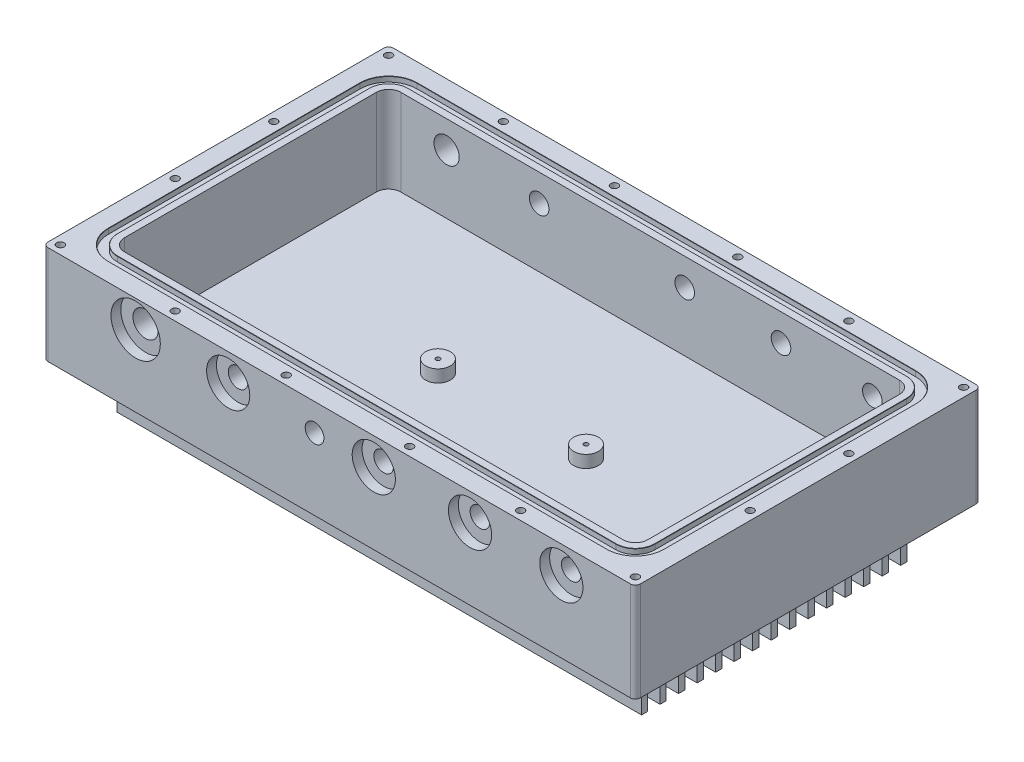
SolidWorks part; units mm, degrees
material "6061 Alloy"
ref_plane "Front Plane" through (0, 0, 0) normal (0, 0, 1) x (1, 0, 0)
ref_plane "Top Plane" through (0, 0, 0) normal (0, 1, 0) x (1, 0, 0)
ref_plane "Right Plane" through (0, 0, 0) normal (1, 0, 0) x (0, 0, -1)
sketch "Sketch1" plane through (0, 0, 0) normal (0, 1, 0) x (1, 0, 0)
  line L1 (0, 0) -> (304.8, 0)
  line L2 (0, 0) -> (0, 177.8)
  line L3 (0, 177.8) -> (304.8, 177.8)
  line L4 (304.8, 0) -> (304.8, 177.8)
  dimension "D1" = 304.8
  dimension "D2" = 177.8
extrude "Boss-Extrude1" add sketch "Sketch1" along normal blind 76.2
sketch "Sketch2" plane through (0, 76.2, 0) normal (0, 1, 0) x (1, 0, 0)
  line L14 (17.78, 17.78) -> (287.02, 17.78)
  line L15 (287.02, 17.78) -> (287.02, 160.02)
  line L16 (287.02, 160.02) -> (17.78, 160.02)
  line L17 (17.78, 160.02) -> (17.78, 17.78)
  line L18 (17.78, 17.78) -> (287.02, 17.78)
  line L19 (287.02, 17.78) -> (287.02, 160.02)
  line L20 (287.02, 160.02) -> (17.78, 160.02)
  line L21 (17.78, 160.02) -> (17.78, 17.78)
  dimension "D1" = 17.78
extrude "Cut-Extrude1" cut sketch "Sketch2" against normal blind 38.1
sketch "Sketch3" plane through (0, 0, 0) normal (0, -1, 0) x (1, 0, 0)
  line L0 (304.8, -177.8) -> (0, -177.8) construction
  line L1 (304.8, 0) -> (304.8, -177.8) construction
  line L2 (0, 0) -> (304.8, 0) construction
  line L3 (0, -177.8) -> (0, 0) construction
  line L4 (304.8, -177.8) -> (0, -177.8)
  line L5 (304.8, 0) -> (304.8, -177.8)
  line L6 (0, 0) -> (304.8, 0)
  line L7 (0, -177.8) -> (0, 0)
  line L8 (17.4625, -160.3375) -> (17.4625, -17.4625)
  line L9 (17.4625, -17.4625) -> (287.3375, -17.4625)
  line L10 (287.3375, -17.4625) -> (287.3375, -160.3375)
  line L11 (287.3375, -160.3375) -> (17.4625, -160.3375)
  dimension "D1" = 17.4625
extrude "Cut-Extrude2" cut sketch "Sketch3" against normal blind 25.4
sketch "Sketch4" plane through (287.3375, 0, 0) normal (1, 0, 0) x (0, 0, -1)
  line L0 (88.9, 0) -> (88.9, 25.4) construction
  line L1 (160.3375, 0) -> (17.4625, 0) construction
  line L2 (160.3375, 25.4) -> (17.4625, 25.4) construction
  line L3 (87.3125, 0) -> (90.4875, 0)
  line L4 (90.4875, 0) -> (90.4875, 25.4)
  line L5 (177.8, 25.4) -> (0, 25.4) construction
  line L6 (90.4875, 25.4) -> (96.8375, 25.4)
  line L7 (96.8375, 25.4) -> (96.8375, 0)
  line L8 (96.8375, 0) -> (100.0125, 0)
  line L9 (100.0125, 0) -> (100.0125, 25.4)
  line L10 (100.0125, 25.4) -> (106.3625, 25.4)
  line L11 (106.3625, 25.4) -> (106.3625, 0)
  line L12 (106.3625, 0) -> (109.5375, 0)
  line L13 (109.5375, 0) -> (109.5375, 25.4)
  line L14 (109.5375, 25.4) -> (115.8875, 25.4)
  line L15 (115.8875, 25.4) -> (115.8875, 0)
  line L16 (115.8875, 0) -> (119.0625, 0)
  line L17 (119.0625, 0) -> (119.0625, 25.4)
  line L18 (119.0625, 25.4) -> (125.4125, 25.4)
  line L19 (125.4125, 25.4) -> (125.4125, 0)
  line L20 (125.4125, 0) -> (128.5875, 0)
  line L21 (128.5875, 0) -> (128.5875, 25.4)
  line L22 (128.5875, 25.4) -> (134.9375, 25.4)
  line L23 (134.9375, 25.4) -> (134.9375, 0)
  line L24 (134.9375, 0) -> (138.1125, 0)
  line L25 (138.1125, 0) -> (138.1125, 25.4)
  line L26 (138.1125, 25.4) -> (144.4625, 25.4)
  line L27 (144.4625, 25.4) -> (144.4625, 0)
  line L28 (144.4625, 0) -> (147.6375, 0)
  line L29 (147.6375, 0) -> (147.6375, 25.4)
  line L30 (147.6375, 25.4) -> (153.9875, 25.4)
  line L31 (153.9875, 25.4) -> (153.9875, 0)
  line L32 (153.9875, 0) -> (157.1625, 0)
  line L33 (157.1625, 0) -> (157.1625, 25.4)
  line L34 (157.1625, 25.4) -> (163.5125, 25.4)
  line L35 (163.5125, 25.4) -> (163.5125, 0)
  line L36 (163.5125, 0) -> (166.6875, 0)
  line L37 (166.6875, 0) -> (166.6875, 25.4)
  line L38 (166.6875, 25.4) -> (173.0375, 25.4)
  line L39 (173.0375, 25.4) -> (173.0375, 0)
  line L40 (4.7625, 25.4) -> (4.7625, 0)
  line L41 (11.1125, 25.4) -> (4.7625, 25.4)
  line L42 (11.1125, 0) -> (11.1125, 25.4)
  line L43 (14.2875, 0) -> (11.1125, 0)
  line L44 (14.2875, 25.4) -> (14.2875, 0)
  line L45 (20.6375, 25.4) -> (14.2875, 25.4)
  line L46 (20.6375, 0) -> (20.6375, 25.4)
  line L47 (23.8125, 0) -> (20.6375, 0)
  line L48 (23.8125, 25.4) -> (23.8125, 0)
  line L49 (30.1625, 25.4) -> (23.8125, 25.4)
  line L50 (30.1625, 0) -> (30.1625, 25.4)
  line L51 (33.3375, 0) -> (30.1625, 0)
  line L52 (33.3375, 25.4) -> (33.3375, 0)
  line L53 (39.6875, 25.4) -> (33.3375, 25.4)
  line L54 (39.6875, 0) -> (39.6875, 25.4)
  line L55 (42.8625, 0) -> (39.6875, 0)
  line L56 (42.8625, 25.4) -> (42.8625, 0)
  line L57 (49.2125, 25.4) -> (42.8625, 25.4)
  line L58 (49.2125, 0) -> (49.2125, 25.4)
  line L59 (52.3875, 0) -> (49.2125, 0)
  line L60 (52.3875, 25.4) -> (52.3875, 0)
  line L61 (58.7375, 25.4) -> (52.3875, 25.4)
  line L62 (58.7375, 0) -> (58.7375, 25.4)
  line L63 (61.9125, 0) -> (58.7375, 0)
  line L64 (61.9125, 25.4) -> (61.9125, 0)
  line L65 (68.2625, 25.4) -> (61.9125, 25.4)
  line L66 (68.2625, 0) -> (68.2625, 25.4)
  line L67 (71.4375, 0) -> (68.2625, 0)
  line L68 (71.4375, 25.4) -> (71.4375, 0)
  line L69 (77.7875, 25.4) -> (71.4375, 25.4)
  line L70 (77.7875, 0) -> (77.7875, 25.4)
  line L71 (80.9625, 0) -> (77.7875, 0)
  line L72 (80.9625, 25.4) -> (80.9625, 0)
  line L73 (87.3125, 25.4) -> (80.9625, 25.4)
  line L74 (87.3125, 0) -> (87.3125, 25.4)
  line L75 (173.0375, 0) -> (176.2125, 0)
  line L76 (176.2125, 0) -> (176.2125, 25.4)
  line L77 (176.2125, 25.4) -> (182.5625, 25.4)
  line L78 (182.5625, 25.4) -> (182.5625, 0)
  line L79 (182.5625, 0) -> (185.7375, 0)
  line L80 (185.7375, 0) -> (185.7375, 25.4)
  line L81 (185.7375, 25.4) -> (192.0875, 25.4)
  line L82 (192.0875, 25.4) -> (192.0875, 0)
  line L83 (192.0875, 0) -> (195.2625, 0)
  line L84 (195.2625, 0) -> (195.2625, 25.4)
  line L85 (195.2625, 25.4) -> (201.6125, 25.4)
  line L86 (201.6125, 25.4) -> (201.6125, 0)
  line L87 (201.6125, 0) -> (204.7875, 0)
  line L88 (204.7875, 0) -> (204.7875, 25.4)
  line L89 (204.7875, 25.4) -> (211.1375, 25.4)
  line L90 (-42.8625, 0) -> (-46.0375, 0)
  line L91 (4.7625, 0) -> (1.5875, 0)
  line L92 (-42.8625, 25.4) -> (-42.8625, 0)
  line L93 (211.1375, 25.4) -> (211.1375, 0)
  line L94 (-26.9875, 0) -> (-26.9875, 25.4)
  line L95 (-23.8125, 0) -> (-26.9875, 0)
  line L96 (-23.8125, 25.4) -> (-23.8125, 0)
  line L97 (-17.4625, 25.4) -> (-23.8125, 25.4)
  line L98 (-17.4625, 0) -> (-17.4625, 25.4)
  line L99 (-14.2875, 0) -> (-17.4625, 0)
  line L100 (-14.2875, 25.4) -> (-14.2875, 0)
  line L101 (-7.9375, 25.4) -> (-14.2875, 25.4)
  line L102 (-7.9375, 0) -> (-7.9375, 25.4)
  line L103 (-4.7625, 0) -> (-7.9375, 0)
  line L104 (-4.7625, 25.4) -> (-4.7625, 0)
  line L105 (1.5875, 25.4) -> (-4.7625, 25.4)
  line L106 (1.5875, 0) -> (1.5875, 25.4)
  line L107 (-36.5125, 25.4) -> (-42.8625, 25.4)
  line L108 (211.1375, 0) -> (214.3125, 0)
  line L109 (214.3125, 0) -> (214.3125, 25.4)
  line L110 (214.3125, 25.4) -> (220.6625, 25.4)
  line L111 (220.6625, 25.4) -> (220.6625, 0)
  line L112 (220.6625, 0) -> (223.8375, 0)
  line L113 (223.8375, 0) -> (223.8375, 25.4)
  line L114 (223.8375, 25.4) -> (230.1875, 25.4)
  line L115 (230.1875, 25.4) -> (230.1875, 0)
  line L116 (-36.5125, 0) -> (-36.5125, 25.4)
  line L117 (-33.3375, 0) -> (-36.5125, 0)
  line L118 (-33.3375, 25.4) -> (-33.3375, 0)
  line L119 (-26.9875, 25.4) -> (-33.3375, 25.4)
  line L120 (-46.0375, 0) -> (-46.0375, 25.4)
  line L121 (-46.0375, 25.4) -> (-52.3875, 25.4)
  line L122 (-52.3875, 25.4) -> (-52.3875, 0)
  line L123 (-52.3875, 0) -> (-52.3875, -16.0515)
  line L124 (-52.3875, -16.0515) -> (230.1875, -16.0515)
  line L125 (230.1875, -16.0515) -> (230.1875, 0)
  dimension "D1" = 1.5875
  dimension "D2" = 3.175
  dimension "D3" = 6.35
extrude "Cut-Extrude3" cut sketch "Sketch4" against normal through all
sketch "Sketch5" plane through (0, 76.2, 0) normal (0, 1, 0) x (1, 0, 0)
  line L0 (304.8, 88.9) -> (0, 88.9) construction
  line L1 (304.8, 0) -> (304.8, 177.8) construction
  line L2 (0, 177.8) -> (0, 0) construction
  line L3 (152.4, 177.8) -> (152.4, 0) construction
  line L4 (304.8, 177.8) -> (0, 177.8) construction
  line L5 (0, 0) -> (304.8, 0) construction
  line L6 (304.8, 173.355) -> (152.4, 173.355) construction
  line L7 (300.355, 177.8) -> (300.355, 0) construction
  point P21 (184.15, 173.355)
  point P33 (241.3, 173.355)
  point P34 (300.355, 173.355)
  point P36 (120.65, 4.445)
  point P37 (63.5, 4.445)
  point P38 (4.445, 4.445)
  point P39 (300.355, 114.3)
  point P41 (4.445, 63.5)
  point P42 (4.445, 114.3)
  point P43 (4.445, 173.355)
  point P44 (63.5, 173.355)
  point P46 (184.15, 4.445)
  point P47 (120.65, 173.355)
  point P51 (300.355, 4.445)
  point P52 (300.355, 63.5)
  point P53 (241.3, 4.445)
  dimension "D1" = 31.75
  dimension "D3" = 25.4
  dimension "D2" = 88.9
  dimension "D4" = 4.445
  dimension "D5" = 4.445
hole_wizard "#10-24 Tapped Hole1" positions "Sketch28" profile "Sketch29" tap size "#10-24" standard "ANSI Inch"
sketch "Sketch28" plane through (0, 76.2, 0) normal (0, 1, 0) x (1, 0, 0)
  point P0 (63.5, 173.355)
  point P3 (120.65, 173.355)
  point P6 (184.15, 173.355)
  point P9 (241.3, 173.355)
  point P15 (241.3, 4.445)
  point P18 (184.15, 4.445)
  point P21 (120.65, 4.445)
  point P24 (63.5, 4.445)
sketch "Sketch29" plane through (63.5, 76.2, -173.355) normal (1, 0, 0) x (0, 0, 1)
  line L0 (0, 0) -> (0, 16.1014)
  line L1 (0, 16.1014) -> (1.8986, 14.9606)
  line L2 (1.8986, 14.9606) -> (1.8986, 0)
  line L5 (1.8986, 0) -> (0, 0)
  line L10 (0, 16.1014) -> (-1.8987, 14.9606) construction
  line L11 (0, -6.35) -> (0, 107.95) construction
  dimension "Tap Drill Dia." = 3.7973
  dimension "Tap Drill Depth" = 14.9606
  dimension "Drill Angle" = 118
cosmetic thread "Hole Thread1" parameters "D1"=9.652, "D2"=4.826
cosmetic thread "Hole Thread2" parameters "D1"=9.652, "D2"=4.826
cosmetic thread "Hole Thread3" parameters "D1"=9.652, "D2"=4.826
cosmetic thread "Hole Thread4" parameters "D1"=9.652, "D2"=4.826
cosmetic thread "Hole Thread5" parameters "D1"=9.652, "D2"=4.826
cosmetic thread "Hole Thread6" parameters "D1"=9.652, "D2"=4.826
cosmetic thread "Hole Thread7" parameters "D1"=9.652, "D2"=4.826
cosmetic thread "Hole Thread8" parameters "D1"=9.652, "D2"=4.826
hole_wizard "#10-24 Tapped Hole2" positions "Sketch30" profile "Sketch31" tap size "#10-24" standard "ANSI Inch" end condition through all
sketch "Sketch30" plane through (0, 76.2, 0) normal (0, 1, 0) x (1, 0, 0)
  point P0 (4.445, 173.355)
  point P3 (4.445, 114.3)
  point P6 (4.445, 63.5)
  point P9 (4.445, 4.445)
  point P12 (300.355, 173.355)
  point P15 (300.355, 114.3)
  point P18 (300.355, 63.5)
  point P21 (300.355, 4.445)
sketch "Sketch31" plane through (4.445, 76.2, -173.355) normal (1, 0, 0) x (0, 0, 1)
  line L0 (0, 0) -> (0, 76.2)
  line L1 (0, 76.2) -> (1.8986, 76.2)
  line L2 (1.8986, 76.2) -> (1.8986, 0)
  line L5 (1.8986, 0) -> (0, 0)
  line L11 (0, -6.35) -> (0, 107.95) construction
  dimension "Thru Tap Drill Dia." = 3.7973
  dimension "Thru Tap Drill Depth" = 76.2
cosmetic thread "Hole Thread9" parameters "D2"=4.826
cosmetic thread "Hole Thread10" parameters "D2"=4.826
cosmetic thread "Hole Thread11" parameters "D2"=4.826
cosmetic thread "Hole Thread12" parameters "D2"=4.826
cosmetic thread "Hole Thread13" parameters "D2"=4.826
cosmetic thread "Hole Thread14" parameters "D2"=4.826
cosmetic thread "Hole Thread15" parameters "D2"=4.826
cosmetic thread "Hole Thread16" parameters "D2"=4.826
sketch "Sketch6" plane through (0, 25.4, 0) normal (0, -1, 0) x (1, 0, 0)
  line L0 (152.4, 0) -> (152.4, -177.8) construction
  line L1 (304.8, 0) -> (0, 0) construction
  line L2 (0, -177.8) -> (304.8, -177.8) construction
  line L3 (298.45, 0) -> (298.45, -177.8) construction
  line L4 (304.8, -88.9) -> (287.3375, -88.9) construction
  line L5 (304.8, -177.8) -> (304.8, 0) construction
  line L6 (287.3375, -90.4875) -> (287.3375, -87.3125) construction
  circle A0 centre (298.45, -63.5) radius 1.9558
  circle A1 centre (298.45, -6.35) radius 1.9558
  circle A2 centre (298.45, -171.45) radius 1.9558
  circle A3 centre (6.35, -171.45) radius 1.9558
  circle A5 centre (6.35, -6.35) radius 1.9558
  circle A6 centre (298.45, -114.3) radius 1.9558
  circle A7 centre (6.35, -114.3) radius 1.9558
  circle A8 centre (6.35, -63.5) radius 1.9558
  dimension "D3" = 3.9116
  dimension "D4" = 57.15
  dimension "D1" = 6.35
  dimension "D2" = 6.35
extrude "Cut-Extrude5" [suppressed] cut sketch "Sketch6" against normal blind 25.4
sketch "Sketch7" plane through (0, 0, 0) normal (-1, 0, 0) x (0, 0, 1)
  line L0 (-88.9, 76.2) -> (-88.9, 38.1) construction
  line L2 (-177.8, 76.2) -> (0, 76.2) construction
  line L3 (-160.02, 38.1) -> (-17.78, 38.1) construction
  line L4 (-134.62, 64.77) -> (-17.78, 64.77) construction
  circle A4 centre (-139.7, 64.77) radius 4.3053
  dimension "D1" = 50.8
  dimension "D2" = 8.6106
  dimension "D4" = 11.43
extrude "Cut-Extrude6" [suppressed] cut sketch "Sketch7" against normal blind 25.4
sketch "Sketch9" plane through (0, 0, -177.8) normal (0, 0, -1) x (-1, 0, 0)
  line L0 (-287.02, 62.23) -> (-53.34, 62.23) construction
  line L1 (-152.4, 76.2) -> (-152.4, 25.4) construction
  line L2 (0, 25.4) -> (-304.8, 25.4) construction
  line L3 (-304.8, 76.2) -> (0, 76.2) construction
  circle A2 centre (-47.625, 62.23) radius 5.4991
  point P19 (-266.7, 62.23)
  point P20 (-219.71, 62.23)
  point P21 (-170.18, 62.23)
  point P22 (-95.25, 62.23)
  point P23 (-47.625, 62.23)
  dimension "D1" = 17.78
  dimension "D6" = 57.15
  dimension "D2" = 104.775
  dimension "D3" = 67.31
  dimension "D4" = 13.97
  dimension "D5" = 114.3
fillet "Fillet1" radius 6.35 4 edges at (17.78, 57.15, -160.02) (17.78, 57.15, -17.78) (287.02, 57.15, -160.02) (287.02, 57.15, -17.78)
sketch "Sketch10" plane through (0, 76.2, 0) normal (0, 1, 0) x (1, 0, 0)
  line L20 (280.67, 168.3258) -> (24.13, 168.3258)
  line L21 (9.4742, 153.67) -> (9.4742, 24.13)
  line L22 (24.13, 9.4742) -> (280.67, 9.4742)
  line L23 (295.3258, 24.13) -> (295.3258, 153.67)
  line L24 (14.097, 153.67) -> (14.097, 24.13)
  line L25 (24.13, 14.097) -> (280.67, 14.097)
  line L26 (290.703, 24.13) -> (290.703, 153.67)
  line L27 (280.67, 163.703) -> (24.13, 163.703)
  line L28 (14.097, 153.67) -> (14.097, 24.13)
  line L29 (24.13, 14.097) -> (280.67, 14.097)
  line L30 (290.703, 24.13) -> (290.703, 153.67)
  line L31 (280.67, 163.703) -> (24.13, 163.703)
  arc A16 (295.3258, 153.67) -> (280.67, 168.3258) centre (280.67, 153.67) ccw
  arc A17 (24.13, 168.3258) -> (9.4742, 153.67) centre (24.13, 153.67) ccw
  arc A18 (9.4742, 24.13) -> (24.13, 9.4742) centre (24.13, 24.13) ccw
  arc A19 (280.67, 9.4742) -> (295.3258, 24.13) centre (280.67, 24.13) ccw
  arc A20 (24.13, 163.703) -> (14.097, 153.67) centre (24.13, 153.67) ccw
  arc A21 (14.097, 24.13) -> (24.13, 14.097) centre (24.13, 24.13) ccw
  arc A22 (280.67, 14.097) -> (290.703, 24.13) centre (280.67, 24.13) ccw
  arc A23 (290.703, 153.67) -> (280.67, 163.703) centre (280.67, 153.67) ccw
  arc A24 (24.13, 163.703) -> (14.097, 153.67) centre (24.13, 153.67) ccw
  arc A25 (14.097, 24.13) -> (24.13, 14.097) centre (24.13, 24.13) ccw
  arc A26 (280.67, 14.097) -> (290.703, 24.13) centre (280.67, 24.13) ccw
  arc A27 (290.703, 153.67) -> (280.67, 163.703) centre (280.67, 153.67) ccw
  dimension "D1" = 3.683
  dimension "D2" = 4.6228
extrude "Cut-Extrude9" cut sketch "Sketch10" against normal blind 2.6416
sketch "Sketch11" plane through (0, 76.2, 0) normal (0, 1, 0) x (1, 0, 0)
  line L0 (152.4, 177.8) -> (152.4, 0) construction
  line L1 (304.8, 177.8) -> (0, 177.8) construction
  line L2 (0, 0) -> (304.8, 0) construction
  line L3 (304.8, 88.9) -> (0, 88.9) construction
  line L4 (304.8, 0) -> (304.8, 177.8) construction
  line L5 (0, 177.8) -> (0, 0) construction
  circle A0 centre (293.37, 166.37) radius 1.9558
  circle A1 centre (293.37, 11.43) radius 1.9558
  circle A2 centre (11.43, 11.43) radius 1.9558
  circle A3 centre (11.43, 166.37) radius 1.9558
  dimension "D1" = 3.9116
  dimension "D2" = 11.43
  dimension "D3" = 11.43
extrude "Cut-Extrude10" [suppressed] cut sketch "Sketch11" against normal blind 25.4
hole_wizard "CBORE for 3/8 Hex Head Bolt2" positions "Sketch20" profile "Sketch21" counterbore size "3/8" standard "ANSI Inch" end condition up to next
sketch "Sketch20" plane through (0, 0, -177.8) normal (0, 0, -1) x (-1, 0, 0)
  point P3 (-266.7, 62.23)
  point P6 (-219.71, 62.23)
  point P9 (-170.18, 62.23)
  point P12 (-95.25, 62.23)
sketch "Sketch21" plane through (266.7, 62.23, -177.8) normal (1, 0, 0) x (0, 1, 0)
  line L0 (0, 0) -> (0, 17.78)
  line L1 (0, 17.78) -> (5.0419, 17.78)
  line L3 (5.0419, 17.78) -> (5.0419, 5.08)
  line L4 (5.0419, 5.08) -> (11.1125, 5.08)
  line L5 (11.1125, 5.08) -> (11.1125, 0)
  line L7 (11.1125, 0) -> (0, 0)
  line L11 (0, -6.35) -> (0, 107.95) construction
  dimension "Thru Hole Dia." = 10.0838
  dimension "Thru Hole Depth" = 17.78
  dimension "C'Bore Dia." = 22.225
  dimension "C'Bore Depth" = 5.08
hole_wizard "CBORE for 1/2 Hex Head Bolt1" positions "Sketch22" profile "Sketch23" counterbore size "1/2" standard "ANSI Inch" end condition up to next
sketch "Sketch22" plane through (0, 0, -177.8) normal (0, 0, -1) x (-1, 0, 0)
  point P0 (-47.625, 62.23)
sketch "Sketch23" plane through (47.625, 62.23, -177.8) normal (1, 0, 0) x (0, 1, 0)
  line L0 (0, 0) -> (0, 17.78)
  line L1 (0, 17.78) -> (6.5024, 17.78)
  line L3 (6.5024, 17.78) -> (6.5024, 5.08)
  line L4 (6.5024, 5.08) -> (12.7, 5.08)
  line L5 (12.7, 5.08) -> (12.7, 0)
  line L7 (12.7, 0) -> (0, 0)
  line L11 (0, -6.35) -> (0, 107.95) construction
  dimension "Thru Hole Dia." = 13.0048
  dimension "Thru Hole Depth" = 17.78
  dimension "C'Bore Dia." = 25.4
  dimension "C'Bore Depth" = 5.08
hole_wizard "CBORE for 3/8 Hex Head Bolt1" positions "Sketch24" profile "Sketch25" counterbore size "3/8" standard "ANSI Inch" end condition up to next
sketch "Sketch24" plane through (0, 0, 0) normal (0, 0, 1) x (1, 0, 0)
  point P10 (95.25, 62.23)
  point P13 (170.18, 62.23)
  point P16 (219.71, 62.23)
  point P19 (266.7, 62.23)
sketch "Sketch25" plane through (95.25, 62.23, 0) normal (1, 0, 0) x (0, -1, 0)
  line L0 (0, 0) -> (0, 17.78)
  line L1 (0, 17.78) -> (5.0419, 17.78)
  line L3 (5.0419, 17.78) -> (5.0419, 5.08)
  line L4 (5.0419, 5.08) -> (11.1125, 5.08)
  line L5 (11.1125, 5.08) -> (11.1125, 0)
  line L7 (11.1125, 0) -> (0, 0)
  line L11 (0, -6.35) -> (0, 107.95) construction
  dimension "Thru Hole Dia." = 10.0838
  dimension "Thru Hole Depth" = 17.78
  dimension "C'Bore Dia." = 22.225
  dimension "C'Bore Depth" = 5.08
sketch "Sketch17" plane through (0, 38.1, 0) normal (0, 1, 0) x (1, 0, 0)
  line L0 (287.02, 88.9) -> (17.78, 88.9) construction
  line L1 (287.02, 24.13) -> (287.02, 153.67) construction
  line L2 (17.78, 153.67) -> (17.78, 24.13) construction
  circle A0 centre (114.3, 88.9) radius 3.175
  circle A1 centre (190.5, 88.9) radius 3.175
  dimension "D1" = 6.35
  dimension "D4" = 76.2
  dimension "D2" = 96.52
  dimension "D3" = 96.52
extrude "Boss-Extrude2" [suppressed] add sketch "Sketch17" along normal blind 38.1
fillet "Fillet2" [suppressed] radius 6.35
chamfer "Chamfer1" distance 0.127 angle 45 16 edges at (295.3258, 76.2, -88.9) (291.0332, 76.2, -164.0332) (291.0332, 76.2, -13.7668) (152.4, 76.2, -168.3258) (152.4, 76.2, -9.4742) (13.7668, 76.2, -164.0332) (13.7668, 76.2, -13.7668) (9.4742, 76.2, -88.9) (290.703, 76.2, -88.9) (287.7644, 76.2, -160.7644) (287.7644, 76.2, -17.0356) (152.4, 76.2, -163.703) (152.4, 76.2, -14.097) (17.0356, 76.2, -160.7644) (17.0356, 76.2, -17.0356) (14.097, 76.2, -88.9)
hole_wizard "1/8 NPT Tapped Hole1" positions "Sketch34" profile "Sketch35" size "1/8" standard "ANSI Inch" end condition up to next
sketch "Sketch34" plane through (0, 0, 0) normal (0, 0, 1) x (1, 0, 0)
  line L0 (152.4, 76.2) -> (152.4, 25.4) construction
  line L1 (0, 76.2) -> (304.8, 76.2) construction
  line L2 (304.8, 25.4) -> (0, 25.4) construction
  point P0 (139.7, 62.23)
  dimension "D1" = 12.7
  dimension "D2" = 13.97
sketch "Sketch35" plane through (139.7, 62.23, 0) normal (1, 0, 0) x (0, -1, 0)
  line L0 (0, 0) -> (0, 17.78)
  line L1 (0, 17.78) -> (4.2164, 17.78)
  line L2 (-4.5374, 9.525) -> (-4.8226, 0) construction
  line L3 (4.2164, 17.78) -> (4.2164, 9.525)
  line L4 (4.2164, 9.525) -> (4.5374, 9.525)
  line L5 (4.5374, 9.525) -> (4.8226, 0)
  line L7 (4.8226, 0) -> (0, 0)
  line L8 (0, -6.35) -> (0, 107.95) construction
  line L11 (-4.2164, 9.525) -> (-4.5374, 9.525) construction
  dimension "Thru Tap Drill Dia." = 8.4328
  dimension "Thru Tap Drill Depth" = 17.78
  dimension "Thread Dia." = 9.6452
  dimension "Thread Angle" = 3.43
  dimension "Thread Depth" = 9.525
cosmetic thread "Hole Thread17" parameters "D1"=9.525, "D2"=10.4428
hole_wizard "#4-40 Tapped Hole1" positions "Sketch36" profile "Sketch37" tap size "#4-40" standard "ANSI Inch"
sketch "Sketch36" plane through (0, 38.1, 0) normal (0, 1, 0) x (1, 0, 0)
  line L0 (152.4, 160.02) -> (152.4, 17.78) construction
  line L1 (280.67, 160.02) -> (24.13, 160.02) construction
  line L2 (24.13, 17.78) -> (280.67, 17.78) construction
  line L4 (17.78, 88.9) -> (287.02, 88.9) construction
  line L5 (17.78, 153.67) -> (17.78, 24.13) construction
  line L6 (287.02, 24.13) -> (287.02, 153.67) construction
  point P0 (114.3, 88.9)
  point P2 (190.5, 88.9)
  dimension "D1" = 76.2
sketch "Sketch37" plane through (114.3, 38.1, -88.9) normal (1, 0, 0) x (0, 0, 1)
  line L0 (0, 0) -> (0, 8.2738)
  line L1 (0, 8.2738) -> (1.1303, 7.5946)
  line L2 (1.1303, 7.5946) -> (1.1303, 0)
  line L5 (1.1303, 0) -> (0, 0)
  line L10 (0, 8.2738) -> (-1.1303, 7.5946) construction
  line L11 (0, -6.35) -> (0, 107.95) construction
  dimension "Tap Drill Dia." = 2.2606
  dimension "Tap Drill Depth" = 7.5946
  dimension "Drill Angle" = 118
cosmetic thread "Hole Thread18" parameters "D1"=5.6896, "D2"=2.8448
cosmetic thread "Hole Thread19" parameters "D1"=5.6896, "D2"=2.8448
sketch "Sketch38" plane through (0, 38.1, 0) normal (0, 1, 0) x (1, 0, 0)
  line L0 (17.78, 153.67) -> (17.78, 24.13) construction
  line L1 (24.13, 17.78) -> (280.67, 17.78) construction
  line L2 (287.02, 24.13) -> (287.02, 153.67) construction
  line L3 (280.67, 160.02) -> (24.13, 160.02) construction
  line L4 (17.78, 153.67) -> (17.78, 24.13)
  line L5 (24.13, 17.78) -> (280.67, 17.78)
  line L6 (287.02, 24.13) -> (287.02, 153.67)
  line L7 (280.67, 160.02) -> (24.13, 160.02)
  arc A0 (24.13, 160.02) -> (17.78, 153.67) centre (24.13, 153.67) ccw construction
  arc A1 (17.78, 24.13) -> (24.13, 17.78) centre (24.13, 24.13) ccw construction
  arc A2 (280.67, 17.78) -> (287.02, 24.13) centre (280.67, 24.13) ccw construction
  arc A3 (287.02, 153.67) -> (280.67, 160.02) centre (280.67, 153.67) ccw construction
  arc A4 (24.13, 160.02) -> (17.78, 153.67) centre (24.13, 153.67) ccw
  arc A5 (17.78, 24.13) -> (24.13, 17.78) centre (24.13, 24.13) ccw
  arc A6 (280.67, 17.78) -> (287.02, 24.13) centre (280.67, 24.13) ccw
  arc A7 (287.02, 153.67) -> (280.67, 160.02) centre (280.67, 153.67) ccw
  circle A8 centre (190.5, 88.9) radius 6.35
  circle A9 centre (114.3, 88.9) radius 6.35
  dimension "D1" = 12.7
extrude "Cut-Extrude11" cut sketch "Sketch38" against normal blind 6.35
fillet "Fillet3" radius 2.54 4 edges at (0, 50.8, -177.8) (304.8, 50.8, 0) (0, 50.8, 0) (304.8, 50.8, -177.8)
sketch "Sketch39" plane through (0, 0, 0) normal (0, 0, 1) x (1, 0, 0)
  circle A0 centre (47.625, 62.23) radius 6.5024 construction
  circle A1 centre (47.625, 62.23) radius 6.5024
extrude "Cut-Extrude12" cut sketch "Sketch39" against normal up to next
sketch "Sketch40" plane through (0, 0, 0) normal (0, 0, 1) x (1, 0, 0)
  circle A0 centre (47.625, 62.23) radius 12.7 construction
  circle A1 centre (47.625, 62.23) radius 12.7
extrude "Cut-Extrude13" cut sketch "Sketch40" against normal blind 5.08
